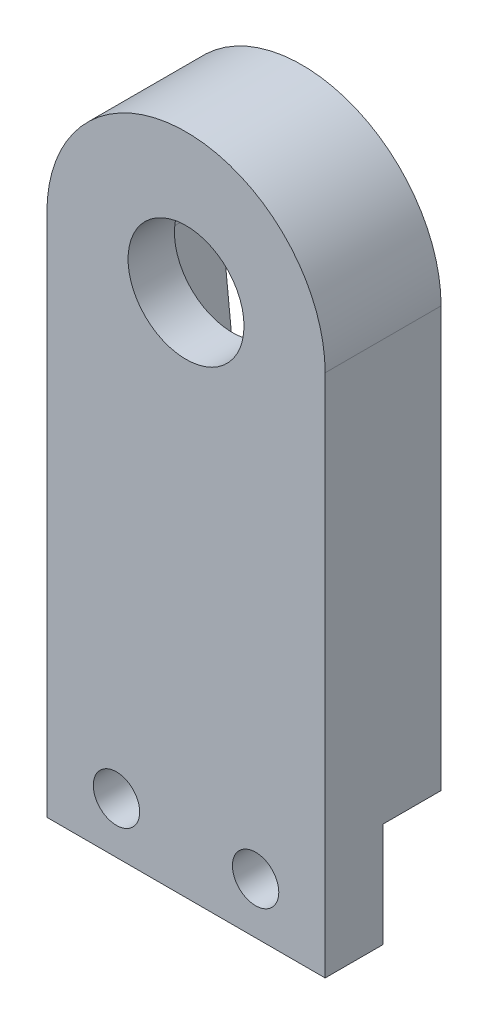
SolidWorks part; units mm, degrees
ref_plane "Front Plane" through (0, 0, 0) normal (0, 0, 1) x (1, 0, 0)
ref_plane "Top Plane" through (0, 0, 0) normal (0, 1, 0) x (1, 0, 0)
ref_plane "Right Plane" through (0, 0, 0) normal (1, 0, 0) x (0, 0, -1)
sketch "Sketch1" plane through (0, 0, 0) normal (0, 0, 1) x (1, 0, 0)
  line L1 (-31.4294, 280.3884) -> (-43.4294, 280.3884)
  line L2 (-31.4294, 280.3884) -> (-31.4294, 302.9935)
  line L3 (-31.4294, 302.9935) -> (-43.4294, 302.9935)
  line L4 (-43.4294, 280.3884) -> (-43.4294, 302.9935)
  dimension "D1" = 22.605
extrude "Boss-Extrude1" add sketch "Sketch1" along normal blind 5 separate body
sketch "Sketch3" plane through (0, 0, 0) normal (0, 0, 1) x (1, 0, 0)
  line L0 (-31.4294, 302.9935) -> (-43.4294, 302.9935) construction
  line L2 (-31.4294, 302.9935) -> (-43.4294, 302.9935)
  arc A0 (-31.4294, 302.9935) -> (-43.4294, 302.9935) centre (-37.4294, 302.9935) ccw
extrude "Boss-Extrude2" add sketch "Sketch3" along normal blind 5
sketch "Sketch4" plane through (0, 0, 0) normal (0, 0, 1) x (1, 0, 0)
  circle A0 centre (-37.4294, 302.9935) radius 2.5
  dimension "D1" = 5
extrude "Cut-Extrude3" cut sketch "Sketch4" along normal blind 5
sketch "Sketch6" plane through (0, 0, 0) normal (0, 0, 1) x (1, 0, 0)
  line L0 (-33.8091, 303.0644) -> (-35.2916, 288.6618)
  line L1 (-40.962, 302.1982) -> (-39.5672, 288.6618)
  arc A0 (-35.2916, 288.6618) -> (-39.5672, 288.6618) centre (-37.4294, 288.8818) cw
  arc A1 (-33.8091, 303.0644) -> (-40.962, 302.1982) centre (-37.4294, 302.9935) ccw
extrude "Cut-Extrude7" cut sketch "Sketch6" along normal blind 3 contours L0 A0 L1 A1
sketch "Sketch10" plane through (0, 0, 0) normal (0, 0, 1) x (1, 0, 0)
  line L1 (-31.4294, 280.3884) -> (-43.4294, 280.3884)
  line L2 (-31.4294, 280.3884) -> (-31.4294, 284.8884)
  line L3 (-31.4294, 284.8884) -> (-43.4294, 284.8884)
  line L4 (-43.4294, 280.3884) -> (-43.4294, 284.8884)
  dimension "D1" = 4.5
extrude "Cut-Extrude8" cut sketch "Sketch10" along normal blind 2.5 contours L3 L4 L1 L2
sketch "Sketch12" plane through (0, 0, 0) normal (0, 0, 1) x (1, 0, 0)
  line L0 (-31.4294, 280.3884) -> (-43.4294, 280.3884) construction
  line L1 (-43.4294, 280.3884) -> (-43.4294, 284.8884) construction
  line L2 (-31.4294, 280.3884) -> (-31.4294, 284.8884) construction
  circle A0 centre (-34.4294, 282.5884) radius 1
  circle A1 centre (-40.4294, 282.5884) radius 1
  dimension "D1" = 2
  dimension "D2" = 2
  dimension "D3" = 2.2
  dimension "D4" = 2.2
  dimension "D5" = 3
  dimension "D6" = 3
extrude "Cut-Extrude9" cut sketch "Sketch12" along normal blind 5
